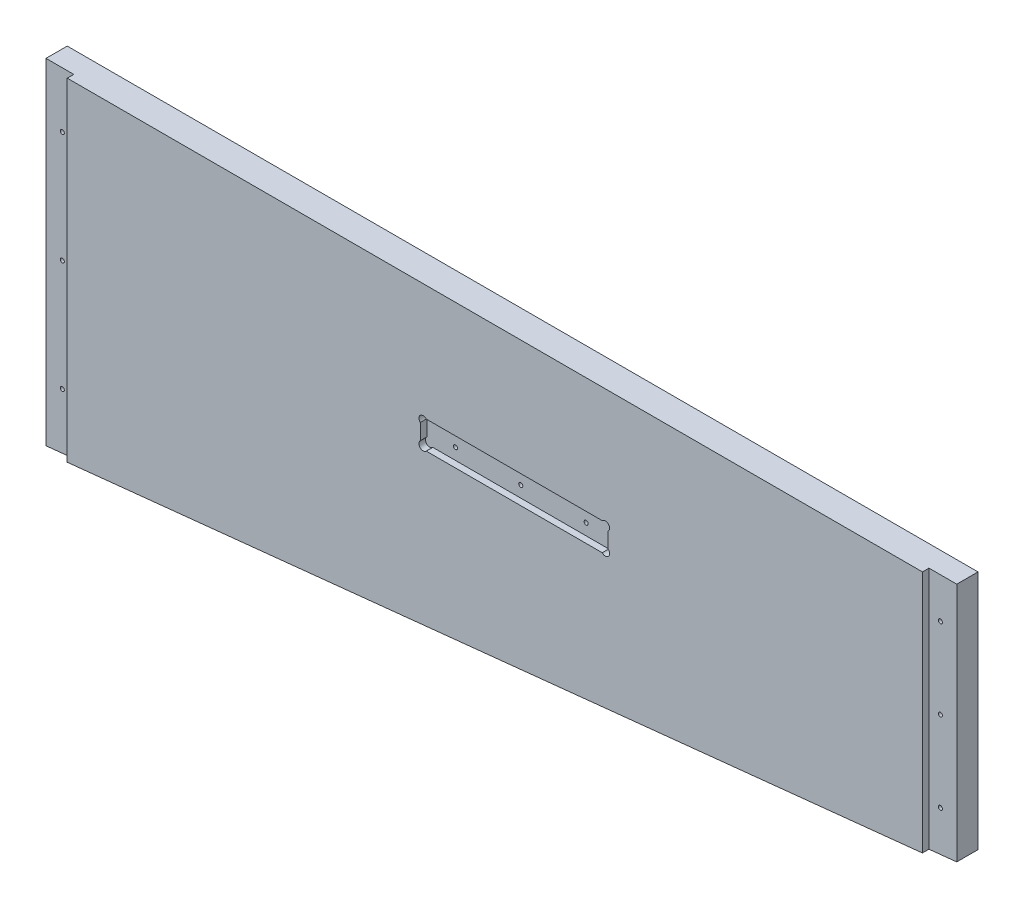
SolidWorks part; units mm, degrees
material "Pine"
ref_plane "Front Plane" through (0, 0, 0) normal (0, 0, 1) x (1, 0, 0)
ref_plane "Top Plane" through (0, 0, 0) normal (0, 1, 0) x (1, 0, 0)
ref_plane "Right Plane" through (0, 0, 0) normal (1, 0, 0) x (0, 0, -1)
sketch "Sketch1" plane through (0, 0, 0) normal (0, 0, 1) x (1, 0, 0)
  line L0 (-163.9887, -5335.905) -> (-163.9887, -5432.425)
  line L1 (-102.87, -5350.891) -> (-33.02, -5350.891)
  line L2 (-111.8235, -5341.9375) -> (-111.8235, -5334)
  line L3 (-24.0665, -5341.9375) -> (-24.0665, -5334)
  line L4 (-298.9262, -5332.73) -> (-167.1637, -5332.73)
  line L5 (-167.1637, -5435.6) -> (-298.9262, -5435.6)
  line L6 (-302.1012, -5432.425) -> (-302.1012, -5335.905)
  line L7 (-107.6325, -5329.809) -> (-28.2575, -5329.809)
  line L8 (174.9425, -5308.6) -> (174.9425, -5581.65)
  line L9 (449.2625, -5413.1661) -> (449.2625, -5421.9659)
  line L10 (595.3125, -5421.9659) -> (595.3125, -5413.1661)
  line L11 (839.47, -5509.5521) -> (839.47, -5307.6729)
  line L12 (839.47, -5307.6729) -> (863.6, -5307.6729)
  line L13 (839.47, -5509.5521) -> (863.6, -5509.5521)
  line L14 (863.6, -5509.5521) -> (863.6, -5307.6729)
  line L15 (-354.2665, -5341.9375) -> (-354.2665, -5334)
  line L16 (-100.8856, -5889.625) -> (-50.0856, -5889.625)
  line L17 (-104.0606, -5969) -> (-104.0606, -5892.8)
  line L18 (-46.9106, -5892.8) -> (-46.9106, -5969)
  line L19 (-50.0856, -5972.175) -> (-100.8856, -5972.175)
  line L20 (-100.8856, -5848.35) -> (-50.0856, -5848.35)
  line L21 (857.25, -5502.275) -> (157.1625, -5575.3)
  line L22 (857.25, -5314.95) -> (857.25, -5502.275)
  line L23 (157.1625, -5314.95) -> (157.1625, -5575.3)
  line L24 (857.25, -5314.95) -> (157.1625, -5314.95)
  line L25 (150.8125, -5308.6) -> (174.9425, -5308.6)
  line L26 (174.9425, -5581.65) -> (150.8125, -5581.65)
  line L27 (137.16, -5314.95) -> (137.16, -5502.275)
  line L28 (150.8125, -5581.65) -> (150.8125, -5308.6)
  line L29 (590.8224, -5408.676) -> (453.7526, -5408.676)
  line L30 (453.7526, -5426.456) -> (590.8224, -5426.456)
  line L31 (137.16, -6013.45) -> (137.16, -5867.4)
  line L32 (150.8125, -5746.75) -> (150.8125, -6019.8)
  line L33 (143.51, -5639.9938) -> (143.51, -5654.294)
  line L34 (590.8224, -5919.724) -> (453.7526, -5919.724)
  line L35 (453.7526, -5901.944) -> (590.8224, -5901.944)
  line L36 (449.2625, -5915.2339) -> (449.2625, -5906.4341)
  line L37 (174.9425, -6019.8) -> (174.9425, -5746.75)
  line L38 (595.3125, -5906.4341) -> (595.3125, -5915.2339)
  line L39 (839.47, -5818.8479) -> (839.47, -6020.7271)
  line L40 (839.47, -5818.8479) -> (863.6, -5818.8479)
  line L41 (863.6, -5818.8479) -> (863.6, -6020.7271)
  line L42 (839.47, -6020.7271) -> (863.6, -6020.7271)
  line L43 (-155.8782, -5867.4) -> (-603.25, -5867.4)
  line L44 (-433.07, -5350.891) -> (-363.22, -5350.891)
  line L45 (-437.8325, -5329.809) -> (-358.4575, -5329.809)
  line L46 (889, -6045.2) -> (-635, -6045.2)
  line L47 (-635, -5283.2) -> (889, -5283.2)
  line L48 (-635, -6045.2) -> (-635, -5283.2)
  line L49 (889, -5283.2) -> (889, -6045.2)
  line L50 (137.16, -5502.275) -> (-603.25, -5502.275)
  line L51 (-603.25, -5314.95) -> (137.16, -5314.95)
  line L52 (143.51, -5654.294) -> (-609.6, -5654.294)
  line L53 (-609.6, -5639.9938) -> (143.51, -5639.9938)
  line L54 (137.16, -5536.0062) -> (-603.25, -5536.0062)
  line L55 (-603.25, -5794.375) -> (137.16, -5794.375)
  line L56 (-603.25, -6013.45) -> (137.16, -6013.45)
  line L57 (-603.25, -5536.0062) -> (-603.25, -5794.375)
  line L58 (137.16, -5794.375) -> (137.16, -5536.0062)
  line L59 (-609.6, -5654.294) -> (-609.6, -5639.9938)
  line L60 (-603.25, -5867.4) -> (-603.25, -6013.45)
  line L61 (-603.25, -5314.95) -> (-603.25, -5502.275)
  line L62 (-442.0235, -5341.9375) -> (-442.0235, -5334)
  line L63 (857.25, -5826.125) -> (157.1625, -5753.1)
  line L64 (857.25, -6013.45) -> (857.25, -5826.125)
  line L65 (157.1625, -6013.45) -> (157.1625, -5753.1)
  line L66 (857.25, -6013.45) -> (157.1625, -6013.45)
  line L67 (174.9425, -5746.75) -> (150.8125, -5746.75)
  line L68 (150.8125, -6019.8) -> (174.9425, -6019.8)
  line L69 (137.16, -5867.4) -> (4.907, -5867.4)
  circle A0 centre (-36.195, -5484.0124) radius 1.5875
  arc A1 (-298.9262, -5332.73) -> (-302.1012, -5335.905) centre (-298.9262, -5335.905) ccw
  arc A2 (-302.1012, -5432.425) -> (-298.9262, -5435.6) centre (-298.9262, -5432.425) ccw
  arc A3 (-163.9887, -5335.905) -> (-167.1637, -5332.73) centre (-167.1637, -5335.905) ccw
  arc A4 (-167.1637, -5435.6) -> (-163.9887, -5432.425) centre (-167.1637, -5432.425) ccw
  arc A5 (-111.8235, -5341.9375) -> (-102.87, -5350.891) centre (-102.87, -5341.9375) ccw
  arc A6 (-107.6325, -5329.809) -> (-111.8235, -5334) centre (-107.6325, -5334) ccw
  circle A7 centre (166.0525, -5444.6613) radius 1.5875
  circle A8 centre (166.0525, -5358.1871) radius 1.5875
  circle A9 centre (471.4875, -5417.566) radius 1.5875
  arc A10 (453.7526, -5408.676) -> (449.2625, -5413.1661) centre (451.5076, -5410.9211) ccw
  arc A11 (449.2625, -5421.9659) -> (453.7526, -5426.456) centre (451.5076, -5424.2109) ccw
  circle A12 centre (522.2875, -5417.566) radius 1.5875
  circle A13 centre (573.0875, -5417.566) radius 1.5875
  arc A14 (590.8224, -5426.456) -> (595.3125, -5421.9659) centre (593.0674, -5424.2109) ccw
  arc A15 (595.3125, -5413.1661) -> (590.8224, -5408.676) centre (593.0674, -5410.9211) ccw
  circle A16 centre (848.36, -5471.8269) radius 1.5875
  circle A17 centre (848.36, -5409.0762) radius 1.5875
  circle A18 centre (848.36, -5346.3254) radius 1.5875
  arc A19 (-363.22, -5350.891) -> (-354.2665, -5341.9375) centre (-363.22, -5341.9375) ccw
  arc A20 (-354.2665, -5334) -> (-358.4575, -5329.809) centre (-358.4575, -5334) ccw
  arc A21 (-24.0665, -5334) -> (-28.2575, -5329.809) centre (-28.2575, -5334) ccw
  arc A22 (-33.02, -5350.891) -> (-24.0665, -5341.9375) centre (-33.02, -5341.9375) ccw
  circle A23 centre (-86.995, -5484.0124) radius 1.5875
  circle A24 centre (-333.4544, -5894.07) radius 2.54
  circle A25 centre (-333.4544, -5994.4) radius 2.54
  arc A26 (-104.0606, -5969) -> (-100.8856, -5972.175) centre (-100.8856, -5969) ccw
  arc A27 (-50.0856, -5972.175) -> (-46.9106, -5969) centre (-50.0856, -5969) ccw
  arc A28 (-100.8856, -5848.35) -> (-128.3819, -5857.875) centre (-100.8856, -5892.8) ccw
  arc A29 (-155.8782, -5867.4) -> (-128.3819, -5857.875) centre (-155.8782, -5822.95) ccw
  arc A30 (-22.5893, -5857.875) -> (-50.0856, -5848.35) centre (-50.0856, -5892.8) ccw
  circle A31 centre (-132.6356, -5894.07) radius 2.54
  circle A32 centre (-132.6356, -5994.4) radius 2.54
  arc A33 (-46.9106, -5892.8) -> (-50.0856, -5889.625) centre (-50.0856, -5892.8) ccw
  arc A34 (-100.8856, -5889.625) -> (-104.0606, -5892.8) centre (-100.8856, -5892.8) ccw
  arc A35 (-22.5893, -5857.875) -> (4.907, -5867.4) centre (4.907, -5822.95) ccw
  circle A36 centre (166.0525, -5531.1356) radius 1.5875
  arc A37 (449.2625, -5915.2339) -> (453.7526, -5919.724) centre (451.5076, -5917.4789) ccw
  arc A38 (453.7526, -5901.944) -> (449.2625, -5906.4341) centre (451.5076, -5904.1891) ccw
  circle A39 centre (166.0525, -5797.2644) radius 1.5875
  circle A40 centre (166.0525, -5883.7387) radius 1.5875
  circle A41 centre (166.0525, -5970.2129) radius 1.5875
  circle A42 centre (471.4875, -5910.834) radius 1.5875
  circle A43 centre (522.2875, -5910.834) radius 1.5875
  circle A44 centre (573.0875, -5910.834) radius 1.5875
  arc A45 (595.3125, -5906.4341) -> (590.8224, -5901.944) centre (593.0674, -5904.1891) ccw
  arc A46 (590.8224, -5919.724) -> (595.3125, -5915.2339) centre (593.0674, -5917.4789) ccw
  circle A47 centre (848.36, -5919.3238) radius 1.5875
  circle A48 centre (848.36, -5982.0746) radius 1.5875
  circle A49 centre (848.36, -5856.5731) radius 1.5875
  arc A50 (-437.8325, -5329.809) -> (-442.0235, -5334) centre (-437.8325, -5334) ccw
  circle A51 centre (-429.895, -5484.0124) radius 1.5875
  arc A52 (-442.0235, -5341.9375) -> (-433.07, -5350.891) centre (-433.07, -5341.9375) ccw
  circle A53 centre (-379.095, -5484.0124) radius 1.5875
sketch "Sketch2" plane through (0, 0, 0) normal (0, 0, 1) x (1, 0, 0)
  line L0 (839.47, -5504.1296) -> (839.47, -5314.95)
  line L1 (839.47, -5314.95) -> (174.9425, -5314.95)
  line L2 (174.9425, -5314.95) -> (174.9425, -5573.4454)
  line L3 (174.9425, -5573.4454) -> (839.47, -5504.1296)
  line L4 (174.9425, -5308.6) -> (174.9425, -5581.65) construction
  line L5 (857.25, -5314.95) -> (157.1625, -5314.95) construction
  line L6 (839.47, -5509.5521) -> (839.47, -5307.6729) construction
extrude "Extrude1" add sketch "Sketch2" against normal blind 21.59
sketch "Sketch7" plane through (0, 0, -21.59) normal (0, 0, -1) x (-1, 0, 0)
  line L0 (-174.9425, -5314.95) -> (-153.3525, -5314.95)
  line L1 (-153.3525, -5314.95) -> (-153.3525, -5575.6974)
  line L2 (-153.3525, -5575.6974) -> (-174.9425, -5573.4454)
  line L3 (-174.9425, -5573.4454) -> (-174.9425, -5314.95)
  line L4 (-839.47, -5314.95) -> (-861.06, -5314.95)
  line L5 (-861.06, -5314.95) -> (-861.06, -5501.8776)
  line L6 (-861.06, -5501.8776) -> (-839.47, -5504.1296)
  line L7 (-839.47, -5504.1296) -> (-839.47, -5314.95)
  line L8 (-857.25, -5502.275) -> (-157.1625, -5575.3) construction
  dimension "D1" = 21.59
  dimension "D2" = 21.59
extrude "Extrude2" add sketch "Sketch7" against normal blind 16.51
sketch "Sketch4" plane through (0, 0, 0) normal (0, 0, 1) x (1, 0, 0)
  line L12 (449.2625, -5426.456) -> (595.3125, -5426.456)
  line L13 (595.3125, -5404.866) -> (595.3125, -5426.456)
  line L14 (595.3125, -5404.866) -> (449.2625, -5404.866)
  line L15 (449.2625, -5404.866) -> (449.2625, -5426.456)
  dimension "D1" = 21.59
extrude "Cut-Extrude2" cut sketch "Sketch4" against normal blind 5.08
sketch "Sketch6" plane through (0, 0, 0) normal (0, 0, 1) x (1, 0, 0)
  line L0 (595.3125, -5426.456) -> (593.0674, -5424.2109) construction
  line L1 (595.3125, -5404.866) -> (593.0674, -5407.1111) construction
  line L2 (449.2625, -5426.456) -> (451.5076, -5424.2109) construction
  line L3 (449.2625, -5404.866) -> (451.5076, -5407.1111) construction
  line L4 (449.2625, -5426.456) -> (595.3125, -5426.456) construction
  line L5 (595.3125, -5404.866) -> (449.2625, -5404.866) construction
  line L6 (449.2625, -5426.456) -> (595.3125, -5426.456) construction
  circle A0 centre (451.5076, -5407.1111) radius 3.302
  circle A1 centre (451.5076, -5424.2109) radius 3.302
  circle A2 centre (593.0674, -5424.2109) radius 3.302
  circle A3 centre (593.0674, -5407.1111) radius 3.302
  dimension "D1" = 45
  dimension "D2" = 45
  dimension "D3" = 3.175
  dimension "D4" = 3.175
  dimension "D5" = 45
  dimension "D6" = 45
  dimension "D7" = 3.175
  dimension "D8" = 3.175
extrude "Cut-Extrude3" cut sketch "Sketch6" against normal up to surface (5.08 mm away) up to face at (522.2875, -5415.661, -5.08)
sketch "Sketch3" plane through (0, 0, 0) normal (0, 0, 1) x (1, 0, 0)
  circle A0 centre (166.0525, -5531.1356) radius 1.5875
  circle A1 centre (166.0525, -5444.6613) radius 1.5875
  circle A2 centre (166.0525, -5358.1871) radius 1.5875
  circle A3 centre (848.36, -5471.8269) radius 1.5875
  circle A4 centre (848.36, -5409.0762) radius 1.5875
  circle A5 centre (848.36, -5346.3254) radius 1.5875
  circle A6 centre (573.0875, -5417.566) radius 1.5875
  circle A7 centre (522.2875, -5417.566) radius 1.5875
  circle A8 centre (471.4875, -5417.566) radius 1.5875
extrude "Cut-Extrude1" cut sketch "Sketch3" against normal up to surface (21.59 mm away) up to face at (507.2062, -5426.8687, -21.59)
